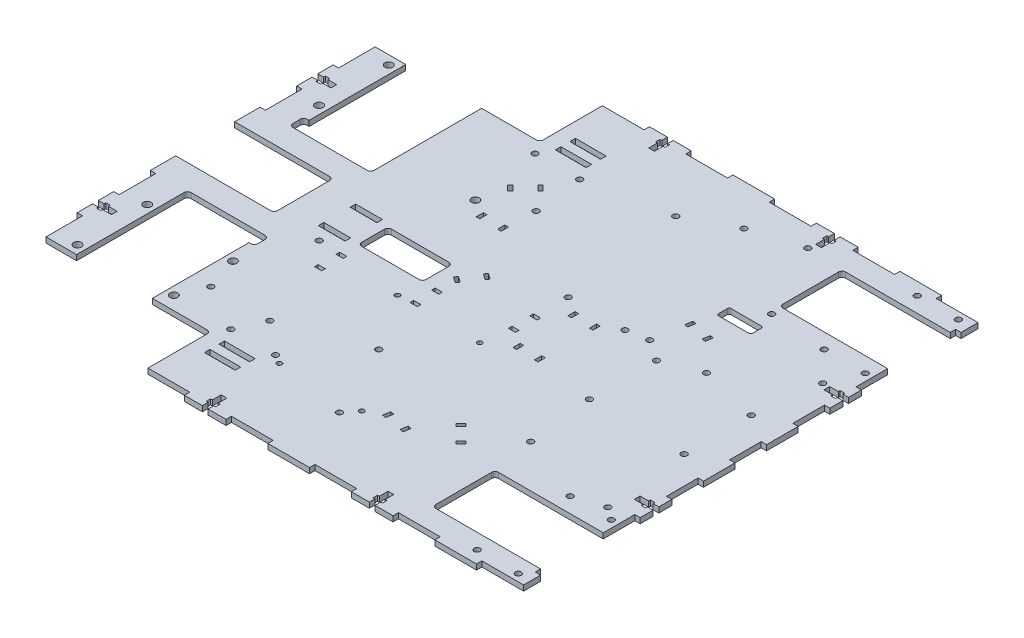
SolidWorks part; units mm, degrees
ref_plane "Front Plane" through (0, 0, 0) normal (0, 0, 1) x (1, 0, 0)
ref_plane "Top Plane" through (0, 0, 0) normal (0, 1, 0) x (1, 0, 0)
ref_plane "Right Plane" through (0, 0, 0) normal (1, 0, 0) x (0, 0, -1)
sketch "Sketch1" plane through (0, 0, 0) normal (0, 1, 0) x (1, 0, 0)
  line L0 (-152.5, 92) -> (-57.5, 92)
  line L5 (-57.5, 92) -> (-57.5, 130)
  line L6 (-57.5, 130) -> (152.5, 130)
  line L7 (152.5, 130) -> (152.5, -130)
  line L8 (152.5, -130) -> (-57.5, -130)
  line L9 (-57.5, -130) -> (-57.5, -92)
  line L10 (-57.5, -92) -> (-152.5, -92)
  line L11 (-152.5, -92) -> (-152.5, 92)
  line L12 (-152.5, 0) -> (152.5, 0) construction
  line L13 (134, -97) -> (134, 97) construction
  line L14 (89, 79.5) -> (152.5, 79.5)
  line L15 (89, 79.5) -> (89, 114.5)
  line L16 (89, 114.5) -> (152.5, 114.5)
  line L17 (152.5, 79.5) -> (152.5, 114.5)
  line L18 (89, 79.5) -> (152.5, 114.5) construction
  line L19 (89, 114.5) -> (152.5, 79.5) construction
  line L20 (89, -114.5) -> (152.5, -114.5)
  line L21 (89, -114.5) -> (89, -79.5)
  line L22 (89, -79.5) -> (152.5, -79.5)
  line L23 (152.5, -114.5) -> (152.5, -79.5)
  line L24 (89, -114.5) -> (152.5, -79.5) construction
  line L25 (89, -79.5) -> (152.5, -114.5) construction
  line L26 (145.5, 71) -> (122.5, 71) construction
  line L27 (145.5, 71) -> (145.5, 123) construction
  line L28 (145.5, 123) -> (122.5, 123) construction
  line L29 (122.5, 71) -> (122.5, 123) construction
  line L30 (145.5, 71) -> (122.5, 123) construction
  line L31 (145.5, 123) -> (122.5, 71) construction
  line L32 (122.5, -123) -> (145.5, -123) construction
  line L33 (122.5, -123) -> (122.5, -71) construction
  line L34 (122.5, -71) -> (145.5, -71) construction
  line L35 (145.5, -123) -> (145.5, -71) construction
  line L36 (122.5, -123) -> (145.5, -71) construction
  line L37 (122.5, -71) -> (145.5, -123) construction
  line L38 (-111.2, 92) -> (-111.2, -92) construction
  line L40 (-132.3981, -30) -> (-90.0019, -30)
  line L41 (-132.3981, -30) -> (-132.3981, -92)
  line L42 (-132.3981, -92) -> (-90.0019, -92)
  line L43 (-90.0019, -30) -> (-90.0019, -92)
  line L44 (-132.3981, -30) -> (-90.0019, -92) construction
  line L45 (-132.3981, -92) -> (-90.0019, -30) construction
  line L50 (-135.3981, 30) -> (-132.3981, 30)
  line L52 (-132.3981, 30) -> (-90.0019, 30)
  line L53 (-132.3981, 30) -> (-132.3981, 92)
  line L54 (-132.3981, 92) -> (-90.0019, 92)
  line L55 (-90.0019, 30) -> (-90.0019, 92)
  line L56 (-132.3981, 30) -> (-90.0019, 92) construction
  line L57 (-132.3981, 92) -> (-90.0019, 30) construction
  line L58 (-135.3981, 30) -> (-135.3981, 38)
  line L59 (-135.3981, 38) -> (-132.3981, 38)
  line L64 (-132.3981, 30) -> (-132.3981, 38)
  line L65 (-87.0019, -38) -> (-90.0019, -38)
  line L86 (-135.3981, 30) -> (-132.3981, 38) construction
  line L87 (-135.3981, 38) -> (-132.3981, 30) construction
  line L88 (-87.0019, -38) -> (-87.0019, -30)
  line L89 (-87.0019, -30) -> (-90.0019, -30)
  line L90 (-90.0019, -38) -> (-90.0019, -30)
  line L91 (-87.0019, -38) -> (-90.0019, -30) construction
  line L92 (-87.0019, -30) -> (-90.0019, -38) construction
  circle A0 centre (122.5, 123) radius 1.65
  circle A1 centre (145.5, 123) radius 1.65
  circle A2 centre (145.5, 71) radius 1.65
  circle A3 centre (122.5, 71) radius 1.65
  circle A4 centre (122.5, -71) radius 1.65
  circle A5 centre (145.5, -71) radius 1.65
  circle A6 centre (122.5, -123) radius 1.65
  circle A7 centre (145.5, -123) radius 1.65
  point P5 (134, 97)
  point P8 (-152.5, 0)
  point P10 (152.5, 0)
  point P12 (0, 0)
  point P13 (120.75, 97)
  point P20 (120.75, -97)
  point P30 (134, -97)
  point P44 (134, 0)
  point P47 (-111.2, -61)
  point P52 (-88.5019, -34)
  point P54 (-133.8981, 34)
  point P61 (-111.2, 61)
  dimension "D11" = 3.3
  dimension "D1" = 305
  dimension "D2" = 260
  dimension "D3" = 38
  dimension "D4" = 95
  dimension "D5" = 35
  dimension "D6" = 52
  dimension "D7" = 23
  dimension "D8" = 7
  dimension "D9" = 7
  dimension "D10" = 45
  dimension "D12" = 41.3
  dimension "D13" = 42.3962
  dimension "D14" = 3
  dimension "D15" = 8
  dimension "D16" = 62
  dimension "D18" = 42.3962
  dimension "D19" = 21.1981
extrude "Base" add sketch "Sketch1" along normal blind 3 contours L21 L22 L7 L14 L15 L16 L6 L5 L0 L11 L10 L9 L8 L20 A7 A6 A5 A4 A3 A2 A1 A0
sketch "Sketch10" plane through (0, 3, 0) normal (0, 1, 0) x (1, 0, 0)
  line L0 (-136.8906, 48) -> (-136.8906, 87) construction
  line L1 (-152.5, 92) -> (-132.3981, 92) construction
  line L2 (-132.3981, 38) -> (-132.3981, 92) construction
  line L4 (-136.8906, -87) -> (-136.8906, -48) construction
  line L5 (-136.8906, -67.5) -> (-132.3981, -67.5) construction
  line L6 (-132.3981, -30) -> (-132.3981, -92) construction
  line L7 (-136.8906, 67.5) -> (-132.3981, 67.5) construction
  line L8 (-136.8906, 87) -> (-136.8906, 92) construction
  line L9 (-136.8906, -87) -> (-136.8906, -92) construction
  line L10 (-132.3981, -92) -> (-152.5, -92) construction
  circle A0 centre (-136.8906, 87) radius 2.175
  circle A1 centre (-136.8906, 48) radius 2.175
  circle A2 centre (-47.3096, 45.8) radius 2.175
  circle A3 centre (-136.8906, -48) radius 2.175
  circle A4 centre (-136.8906, -87) radius 2.175
  circle A5 centre (-85.5093, -84.5) radius 2.175
  circle A6 centre (-85.5093, -51.5) radius 2.175
  dimension "D1" = 4.35
  dimension "D3" = 5
  dimension "D5" = 89.581
  dimension "D6" = 2.2
  dimension "D8" = 2.5
  dimension "D9" = 3.5
  dimension "D2" = 39
  dimension "D4" = 4.4925
  dimension "D7" = 51.3813
extrude "MotorMounts" cut sketch "Sketch10" against normal through all both and the other way through all
sketch "Sketch2" plane through (0, 3, 0) normal (0, 1, 0) x (1, 0, 0)
  line L0 (134, -97) -> (134, 97) construction
  line L1 (81, 18.75) -> (134, 18.75) construction
  line L2 (81, 18.75) -> (81, -18.75) construction
  line L3 (81, -18.75) -> (134, -18.75) construction
  line L4 (134, 18.75) -> (134, -18.75) construction
  line L5 (81, 18.75) -> (134, -18.75) construction
  line L6 (81, -18.75) -> (134, 18.75) construction
  line L9 (138.5, -23.5) -> (76.5, -23.5) construction
  line L10 (138.5, -23.5) -> (138.5, 23.5) construction
  line L11 (138.5, 23.5) -> (76.5, 23.5) construction
  line L12 (76.5, -23.5) -> (76.5, 23.5) construction
  line L13 (138.5, -23.5) -> (76.5, 23.5) construction
  line L14 (138.5, 23.5) -> (76.5, -23.5) construction
  circle A0 centre (81, 18.75) radius 1.65
  circle A1 centre (134, 18.75) radius 1.65
  circle A2 centre (134, -18.75) radius 1.65
  circle A3 centre (81, -18.75) radius 1.65
  point P0 (107.5, 0)
  point P12 (107.5, 0)
  dimension "D3" = 3.3
  dimension "D1" = 37.5
  dimension "D2" = 53
  dimension "D4" = 47
  dimension "D5" = 62
extrude "LineFollow" cut sketch "Sketch2" against normal through all both and the other way through all
sketch "Sketch3" plane through (0, 3, 0) normal (0, 1, 0) x (1, 0, 0)
  line L0 (64.76, 59.286) -> (143.5, 59.286) construction
  line L1 (143.5, 59.286) -> (143.5, -70) construction
  line L2 (143.5, -70) -> (71.491, -70) construction
  line L3 (71.491, -70) -> (64.76, -63.269) construction
  line L4 (64.76, -63.269) -> (64.76, 59.286) construction
  line L5 (69.205, 26.774) -> (100.955, 26.774) construction
  line L6 (85.08, -55.649) -> (85.08, 26.774) construction
  line L7 (138.42, 59.286) -> (138.42, 54.206) construction
  line L8 (138.42, 54.206) -> (143.5, 54.206) construction
  line L9 (143.5, -65.809) -> (138.42, -65.809) construction
  line L10 (138.42, -65.809) -> (138.42, -70) construction
  line L12 (152.5, 79.5) -> (152.5, -79.5) construction
  line L13 (76.64, 57.786) -> (93.64, 57.786)
  line L14 (75.64, 58.786) -> (75.64, 63.786)
  line L15 (76.64, 64.786) -> (93.64, 64.786)
  line L16 (94.64, 58.786) -> (94.64, 63.786)
  line L17 (75.64, 57.786) -> (94.64, 64.786) construction
  line L18 (75.64, 64.786) -> (94.64, 57.786) construction
  circle A0 centre (69.205, 26.774) radius 1.65
  circle A1 centre (100.955, 26.774) radius 1.65
  circle A2 centre (85.08, -55.649) radius 1.65
  circle A3 centre (138.42, 54.206) radius 1.65
  circle A4 centre (138.42, -65.809) radius 1.65
  arc A5 (76.64, 57.786) -> (75.64, 58.786) centre (76.64, 58.786) cw
  arc A6 (93.64, 57.786) -> (94.64, 58.786) centre (93.64, 58.786) ccw
  arc A7 (93.64, 64.786) -> (94.64, 63.786) centre (93.64, 63.786) cw
  arc A8 (75.64, 63.786) -> (76.64, 64.786) centre (76.64, 63.786) cw
  point P4 (85.14, 61.286)
  dimension "D5" = 3.3
  dimension "D18" = 1
  dimension "D1" = 78.74
  dimension "D2" = 129.286
  dimension "D3" = 135
  dimension "D4" = 6.731
  dimension "D6" = 31.75
  dimension "D7" = 82.423
  dimension "D8" = 32.512
  dimension "D9" = 4.445
  dimension "D10" = 5.08
  dimension "D11" = 4.191
  dimension "D12" = 70
  dimension "D13" = 9
  dimension "D14" = 19
  dimension "D15" = 7
  dimension "D16" = 1.5
  dimension "D17" = 20.38
extrude "Mobo" cut sketch "Sketch3" against normal through all both and the other way through all
sketch "Sketch4" plane through (0, 3, 0) normal (0, 1, 0) x (1, 0, 0)
  line L0 (41.553, 107.122) -> (41.553, 24.699) construction
  line L1 (21.106, 121.473) -> (62, 121.473) construction
  line L2 (21.106, 121.473) -> (21.106, 20) construction
  line L3 (21.106, 20) -> (62, 20) construction
  line L4 (62, 121.473) -> (62, 20) construction
  line L5 (21.106, 121.473) -> (62, 20) construction
  line L6 (21.106, 20) -> (62, 121.473) construction
  line L7 (25.678, 24.699) -> (57.428, 24.699) construction
  line L8 (89, 79.5) -> (89, 114.5) construction
  line L9 (-57.5, 130) -> (152.5, 130) construction
  line L10 (-152.5, 0) -> (152.5, 0) construction
  line L11 (-152.5, -92) -> (-152.5, 92) construction
  line L12 (152.5, 79.5) -> (152.5, -79.5) construction
  circle A0 centre (25.678, 24.699) radius 1.65
  circle A1 centre (57.428, 24.699) radius 1.65
  circle A2 centre (41.553, 107.122) radius 1.65
  point P0 (41.553, 70.7365)
  point P9 (41.553, 24.699)
  dimension "D3" = 3.3
  dimension "D1" = 31.75
  dimension "D2" = 82.423
  dimension "D4" = 40.894
  dimension "D5" = 101.473
  dimension "D6" = 4.699
  dimension "D7" = 27
  dimension "D8" = 110
extrude "HBridge" cut sketch "Sketch4" against normal through all both and the other way through all
sketch "Sketch6" plane through (0, 3, 0) normal (0, 1, 0) x (1, 0, 0)
  line L0 (-152.5, -92) -> (-152.5, 92) construction
  line L1 (-58.6638, -8.35) -> (-22.6638, -8.35)
  line L2 (-58.6638, -8.35) -> (-58.6638, 8.35)
  line L3 (-58.6638, 8.35) -> (-22.6638, 8.35)
  line L4 (-22.6638, -8.35) -> (-22.6638, 8.35)
  line L5 (-58.6638, -8.35) -> (-22.6638, 8.35) construction
  line L6 (-58.6638, 8.35) -> (-22.6638, -8.35) construction
  point P0 (-40.6638, 0)
  dimension "D1" = 111.8362
  dimension "D3" = 16.7
  dimension "D6" = 36
extrude "GearClearence" cut sketch "Sketch6" against normal through all both and the other way through all
sketch "Sketch7" plane through (0, 3, 0) normal (0, 1, 0) x (1, 0, 0)
  line L1 (-40.6638, 94.05) -> (-40.6638, 102.15) construction
  line L2 (-78.8576, 10.4502) -> (-63.8576, 10.4502)
  line L4 (-78.8576, 10.4502) -> (-78.8576, 7.3502)
  line L9 (-78.8576, 7.3502) -> (-63.8576, 7.3502)
  line L10 (-63.8576, 10.4502) -> (-63.8576, 7.3502)
  line L15 (-78.8576, 10.4502) -> (-63.8576, 7.3502) construction
  line L16 (-78.8576, 7.3502) -> (-63.8576, 10.4502) construction
  line L21 (-78.8576, -7.3502) -> (-63.8576, -7.3502)
  line L22 (-78.8576, -7.3502) -> (-78.8576, -10.4502)
  line L27 (-78.8576, -10.4502) -> (-63.8576, -10.4502)
  line L28 (-63.8576, -7.3502) -> (-63.8576, -10.4502)
  line L29 (-78.8576, -7.3502) -> (-63.8576, -10.4502) construction
  line L30 (-78.8576, -10.4502) -> (-63.8576, -7.3502) construction
  line L32 (-49.2426, 103.7) -> (-32.0849, 103.7)
  line L33 (-49.2426, 103.7) -> (-49.2426, 100.6)
  line L40 (-49.2426, 100.6) -> (-32.0849, 100.6)
  line L45 (-32.0849, 103.7) -> (-32.0849, 100.6)
  line L62 (-49.2426, 103.7) -> (-32.0849, 100.6) construction
  line L63 (-49.2426, 100.6) -> (-32.0849, 103.7) construction
  line L68 (-49.2427, 95.6) -> (-32.085, 95.6)
  line L69 (-49.2427, 95.6) -> (-49.2427, 92.5)
  line L71 (-49.2427, 92.5) -> (-32.085, 92.5)
  line L84 (-32.085, 95.6) -> (-32.085, 92.5)
  line L89 (-49.2427, 95.6) -> (-32.085, 92.5) construction
  line L90 (-49.2427, 92.5) -> (-32.085, 95.6) construction
  line L95 (-49.2427, -92.5) -> (-32.085, -92.5)
  line L96 (-49.2427, -92.5) -> (-49.2427, -95.6)
  line L97 (-49.2427, -95.6) -> (-32.085, -95.6)
  line L102 (-32.085, -92.5) -> (-32.085, -95.6)
  line L103 (-49.2427, -92.5) -> (-32.085, -95.6) construction
  line L104 (-49.2427, -95.6) -> (-32.085, -92.5) construction
  line L105 (-49.2426, -103.7) -> (-32.0849, -103.7)
  line L106 (-49.2426, -103.7) -> (-49.2426, -100.6)
  line L107 (-49.2426, -100.6) -> (-32.0849, -100.6)
  line L108 (-32.0849, -103.7) -> (-32.0849, -100.6)
  line L109 (-49.2426, -103.7) -> (-32.0849, -100.6) construction
  line L110 (-49.2426, -100.6) -> (-32.0849, -103.7) construction
  line L111 (-40.6638, 94.05) -> (-40.6638, -94.05) construction
  line L112 (-40.6638, -94.05) -> (-40.6638, -102.15) construction
  line L113 (-71.3576, -8.9002) -> (-71.3576, 8.9002) construction
  line L114 (-58.6638, 8.35) -> (-22.6638, 8.35) construction
  line L115 (-53.1638, -85) -> (-28.1638, -85) construction
  line L116 (-53.1638, 85) -> (-28.1638, 85) construction
  line L117 (-40.6638, 85) -> (-40.6638, 92.5) construction
  line L118 (-40.6638, -85) -> (-40.6638, -92.5) construction
  circle A6 centre (-53.1638, 85) radius 1.65
  circle A7 centre (-28.1638, 85) radius 1.65
  circle A8 centre (-28.1638, -85) radius 1.65
  circle A9 centre (-53.1638, -85) radius 1.65
  circle A10 centre (-71.3576, -17.4503) radius 1.65
  point P0 (-71.3576, 8.9002)
  point P5 (-71.3576, -8.9002)
  point P10 (-40.6638, 102.15)
  point P15 (-40.6638, 94.05)
  point P20 (-40.6638, -94.05)
  point P25 (-40.6638, -102.15)
  point P32 (-40.6638, 0)
  point P38 (-71.3576, 0)
  point P42 (-40.6638, 8.35)
  point P52 (-40.6638, -85)
  point P53 (-40.6638, 85)
  dimension "D8" = 3.3
  dimension "D1" = 3.1
  dimension "D2" = 17.1577
  dimension "D3" = 185
  dimension "D4" = 5
  dimension "D5" = 15
  dimension "D6" = 14.7005
  dimension "D7" = 23.1938
  dimension "D9" = 7.5
  dimension "D10" = 25
  dimension "D11" = 7
extrude "GearMounting" cut sketch "Sketch7" against normal through all both and the other way through all
sketch "Sketch5" plane through (0, 3, 0) normal (0, 1, 0) x (1, 0, 0)
  line L0 (-152.5, -92) -> (-152.5, 92) construction
  line L1 (-152.5, 92) -> (-149.5, 92)
  line L2 (-152.5, 92) -> (-152.5, 71.5556)
  line L3 (-152.5, 71.5556) -> (-149.5, 71.5556)
  line L4 (-149.5, 92) -> (-149.5, 71.5556)
  line L5 (-152.5, 51.1111) -> (-149.5, 51.1111)
  line L6 (-152.5, 51.1111) -> (-152.5, 30.6667)
  line L7 (-152.5, 30.6667) -> (-149.5, 30.6667)
  line L8 (-149.5, 51.1111) -> (-149.5, 30.6667)
  line L9 (-132.3981, -92) -> (-152.5, -92) construction
  line L10 (-152.5, 10.2222) -> (-149.5, 10.2222)
  line L11 (-152.5, 10.2222) -> (-152.5, -10.2222)
  line L12 (-152.5, -10.2222) -> (-149.5, -10.2222)
  line L13 (-149.5, 10.2222) -> (-149.5, -10.2222)
  line L14 (-152.5, -30.6667) -> (-149.5, -30.6667)
  line L15 (-152.5, -30.6667) -> (-152.5, -51.1111)
  line L16 (-152.5, -51.1111) -> (-149.5, -51.1111)
  line L17 (-149.5, -30.6667) -> (-149.5, -51.1111)
  line L18 (-152.5, -71.5556) -> (-149.5, -71.5556)
  line L19 (-152.5, -71.5556) -> (-152.5, -92)
  line L20 (-152.5, -92) -> (-149.5, -92)
  line L21 (-149.5, -71.5556) -> (-149.5, -92)
  line L22 (-149.5, 71.5556) -> (-149.5, 51.1111) construction
  line L23 (-149.5, 30.6667) -> (-149.5, 10.2222) construction
  line L24 (-149.5, -10.2222) -> (-149.5, -30.6667) construction
  line L25 (-149.5, -51.1111) -> (-149.5, -71.5556) construction
  line L26 (152.5, 79.5) -> (152.5, -79.5) construction
  line L27 (152.5, 79.5) -> (149.5, 79.5)
  line L28 (152.5, 79.5) -> (152.5, 61.8333)
  line L29 (152.5, 61.8333) -> (149.5, 61.8333)
  line L30 (149.5, 79.5) -> (149.5, 61.8333)
  line L31 (152.5, 44.1667) -> (149.5, 44.1667)
  line L32 (152.5, 44.1667) -> (152.5, 26.5)
  line L33 (152.5, 26.5) -> (149.5, 26.5)
  line L34 (149.5, 44.1667) -> (149.5, 26.5)
  line L35 (149.5, 61.8333) -> (149.5, 44.1667) construction
  line L36 (152.5, 8.8333) -> (149.5, 8.8333)
  line L37 (152.5, 8.8333) -> (152.5, -8.8333)
  line L38 (152.5, -8.8333) -> (149.5, -8.8333)
  line L39 (149.5, 8.8333) -> (149.5, -8.8333)
  line L40 (152.5, -26.5) -> (149.5, -26.5)
  line L41 (152.5, -26.5) -> (152.5, -44.1667)
  line L42 (152.5, -44.1667) -> (149.5, -44.1667)
  line L43 (149.5, -26.5) -> (149.5, -44.1667)
  line L44 (152.5, -79.5) -> (149.5, -79.5)
  line L45 (152.5, -79.5) -> (152.5, -61.8333)
  line L46 (152.5, -61.8333) -> (149.5, -61.8333)
  line L47 (149.5, -79.5) -> (149.5, -61.8333)
  line L48 (149.5, 26.5) -> (149.5, 8.8333) construction
  line L49 (149.5, -8.8333) -> (149.5, -26.5) construction
  line L50 (149.5, -44.1667) -> (149.5, -61.8333) construction
  line L51 (-57.5, 130) -> (152.5, 130) construction
  line L52 (-57.5, 130) -> (-34.1667, 130)
  line L53 (-57.5, 130) -> (-57.5, 127)
  line L54 (-57.5, 127) -> (-34.1667, 127)
  line L55 (-34.1667, 130) -> (-34.1667, 127)
  line L56 (-10.8333, 130) -> (12.5, 130)
  line L57 (-10.8333, 130) -> (-10.8333, 127)
  line L58 (-10.8333, 127) -> (12.5, 127)
  line L59 (12.5, 130) -> (12.5, 127)
  line L60 (152.5, 130) -> (152.5, 114.5) construction
  line L61 (35.8333, 130) -> (59.1667, 130)
  line L62 (35.8333, 130) -> (35.8333, 127)
  line L63 (35.8333, 127) -> (59.1667, 127)
  line L64 (59.1667, 130) -> (59.1667, 127)
  line L65 (82.5, 130) -> (105.8333, 130)
  line L66 (82.5, 130) -> (82.5, 127)
  line L67 (82.5, 127) -> (105.8333, 127)
  line L68 (105.8333, 130) -> (105.8333, 127)
  line L69 (129.1667, 130) -> (152.5, 130)
  line L70 (129.1667, 130) -> (129.1667, 127)
  line L71 (129.1667, 127) -> (152.5, 127)
  line L72 (152.5, 130) -> (152.5, 127)
  line L73 (-34.1667, 127) -> (-10.8333, 127) construction
  line L74 (12.5, 127) -> (35.8333, 127) construction
  line L75 (59.1667, 127) -> (82.5, 127) construction
  line L76 (105.8333, 127) -> (129.1667, 127) construction
  line L77 (89, 114.5) -> (152.5, 114.5) construction
  line L78 (152.5, 117.5) -> (149.5, 117.5)
  line L79 (152.5, 117.5) -> (152.5, 114.5)
  line L80 (152.5, 114.5) -> (149.5, 114.5)
  line L81 (149.5, 117.5) -> (149.5, 114.5)
  line L82 (-1.65, 0) -> (1.65, 0) construction
  line L83 (105.8333, -127) -> (129.1667, -127) construction
  line L84 (59.1667, -127) -> (82.5, -127) construction
  line L85 (12.5, -127) -> (35.8333, -127) construction
  line L86 (-34.1667, -127) -> (-10.8333, -127) construction
  line L87 (149.5, -117.5) -> (149.5, -114.5)
  line L88 (152.5, -114.5) -> (149.5, -114.5)
  line L89 (152.5, -117.5) -> (152.5, -114.5)
  line L90 (152.5, -117.5) -> (149.5, -117.5)
  line L91 (152.5, -130) -> (152.5, -127)
  line L92 (129.1667, -127) -> (152.5, -127)
  line L93 (129.1667, -130) -> (129.1667, -127)
  line L94 (129.1667, -130) -> (152.5, -130)
  line L95 (105.8333, -130) -> (105.8333, -127)
  line L96 (82.5, -127) -> (105.8333, -127)
  line L97 (82.5, -130) -> (82.5, -127)
  line L98 (82.5, -130) -> (105.8333, -130)
  line L99 (59.1667, -130) -> (59.1667, -127)
  line L100 (35.8333, -127) -> (59.1667, -127)
  line L101 (35.8333, -130) -> (35.8333, -127)
  line L102 (35.8333, -130) -> (59.1667, -130)
  line L103 (12.5, -130) -> (12.5, -127)
  line L104 (-10.8333, -127) -> (12.5, -127)
  line L105 (-10.8333, -130) -> (-10.8333, -127)
  line L106 (-10.8333, -130) -> (12.5, -130)
  line L107 (-34.1667, -130) -> (-34.1667, -127)
  line L108 (-57.5, -127) -> (-34.1667, -127)
  line L109 (-57.5, -130) -> (-57.5, -127)
  line L110 (-57.5, -130) -> (-34.1667, -130)
  dimension "D1" = 3
extrude "FingerJoints" cut sketch "Sketch5" against normal through all both and the other way through all
sketch "Sketch8" plane through (0, 3, 0) normal (0, 1, 0) x (1, 0, 0)
  line L0 (-34.1667, 130) -> (-10.8333, 130) construction
  line L1 (-24.1, 119.5) -> (-20.9, 119.5)
  line L2 (-24.1, 119.5) -> (-24.1, 130)
  line L3 (-24.1, 130) -> (-20.9, 130)
  line L4 (-20.9, 119.5) -> (-20.9, 130)
  line L5 (-24.1, 119.5) -> (-20.9, 130) construction
  line L6 (-24.1, 130) -> (-20.9, 119.5) construction
  line L7 (59.1667, 130) -> (82.5, 130) construction
  line L8 (69.2333, 119.5) -> (72.4333, 119.5)
  line L9 (69.2333, 119.5) -> (69.2333, 130)
  line L10 (69.2333, 130) -> (72.4333, 130)
  line L11 (72.4333, 119.5) -> (72.4333, 130)
  line L12 (69.2333, 119.5) -> (72.4333, 130) construction
  line L13 (69.2333, 130) -> (72.4333, 119.5) construction
  line L14 (82.5, -130) -> (59.1667, -130) construction
  line L15 (72.4333, -119.5) -> (69.2333, -119.5)
  line L16 (72.4333, -119.5) -> (72.4333, -130)
  line L17 (72.4333, -130) -> (69.2333, -130)
  line L18 (69.2333, -119.5) -> (69.2333, -130)
  line L19 (72.4333, -119.5) -> (69.2333, -130) construction
  line L20 (72.4333, -130) -> (69.2333, -119.5) construction
  line L21 (-10.8333, -130) -> (-34.1667, -130) construction
  line L22 (-24.1, -119.5) -> (-20.9, -119.5)
  line L23 (-24.1, -119.5) -> (-24.1, -130)
  line L24 (-24.1, -130) -> (-20.9, -130)
  line L25 (-20.9, -119.5) -> (-20.9, -130)
  line L26 (-24.1, -119.5) -> (-20.9, -130) construction
  line L27 (-24.1, -130) -> (-20.9, -119.5) construction
  line L28 (152.5, 61.8333) -> (152.5, 44.1667) construction
  line L29 (142, 54.6) -> (152.5, 54.6)
  line L30 (142, 54.6) -> (142, 51.4)
  line L31 (142, 51.4) -> (152.5, 51.4)
  line L32 (152.5, 54.6) -> (152.5, 51.4)
  line L33 (142, 54.6) -> (152.5, 51.4) construction
  line L34 (142, 51.4) -> (152.5, 54.6) construction
  line L35 (152.5, -44.1667) -> (152.5, -61.8333) construction
  line L36 (142, -51.4) -> (152.5, -51.4)
  line L37 (142, -51.4) -> (142, -54.6)
  line L38 (142, -54.6) -> (152.5, -54.6)
  line L39 (152.5, -51.4) -> (152.5, -54.6)
  line L40 (142, -51.4) -> (152.5, -54.6) construction
  line L41 (142, -54.6) -> (152.5, -51.4) construction
  line L42 (-152.5, 51.1111) -> (-152.5, 71.5556) construction
  line L43 (-142, 59.7333) -> (-152.5, 59.7333)
  line L44 (-142, 59.7333) -> (-142, 62.9333)
  line L45 (-142, 62.9333) -> (-152.5, 62.9333)
  line L46 (-152.5, 59.7333) -> (-152.5, 62.9333)
  line L47 (-142, 59.7333) -> (-152.5, 62.9333) construction
  line L48 (-142, 62.9333) -> (-152.5, 59.7333) construction
  line L49 (-152.5, -71.5556) -> (-152.5, -51.1111) construction
  line L50 (-142, -62.9333) -> (-152.5, -62.9333)
  line L51 (-142, -62.9333) -> (-142, -59.7333)
  line L52 (-142, -59.7333) -> (-152.5, -59.7333)
  line L53 (-152.5, -62.9333) -> (-152.5, -59.7333)
  line L54 (-142, -62.9333) -> (-152.5, -59.7333) construction
  line L55 (-142, -59.7333) -> (-152.5, -62.9333) construction
  line L56 (-22.5, 125.575) -> (-22.5, 130) construction
  line L57 (-25.1, 124.325) -> (-19.9, 124.325)
  line L58 (-25.1, 124.325) -> (-25.1, 126.825)
  line L59 (-25.1, 126.825) -> (-19.9, 126.825)
  line L60 (-19.9, 124.325) -> (-19.9, 126.825)
  line L61 (-25.1, 124.325) -> (-19.9, 126.825) construction
  line L62 (-25.1, 126.825) -> (-19.9, 124.325) construction
  line L63 (68.2333, 126.825) -> (73.4333, 126.825)
  line L64 (68.2333, 126.825) -> (68.2333, 124.325)
  line L65 (68.2333, 124.325) -> (73.4333, 124.325)
  line L66 (73.4333, 126.825) -> (73.4333, 124.325)
  line L67 (68.2333, 126.825) -> (73.4333, 124.325) construction
  line L68 (68.2333, 124.325) -> (73.4333, 126.825) construction
  line L69 (149.325, 50.4) -> (146.825, 50.4)
  line L70 (149.325, 50.4) -> (149.325, 55.6)
  line L71 (149.325, 55.6) -> (146.825, 55.6)
  line L72 (146.825, 50.4) -> (146.825, 55.6)
  line L73 (149.325, 50.4) -> (146.825, 55.6) construction
  line L74 (149.325, 55.6) -> (146.825, 50.4) construction
  line L75 (149.325, -55.6) -> (146.825, -55.6)
  line L76 (149.325, -55.6) -> (149.325, -50.4)
  line L77 (149.325, -50.4) -> (146.825, -50.4)
  line L78 (146.825, -55.6) -> (146.825, -50.4)
  line L79 (149.325, -55.6) -> (146.825, -50.4) construction
  line L80 (149.325, -50.4) -> (146.825, -55.6) construction
  line L81 (68.2333, -126.825) -> (73.4333, -126.825)
  line L82 (68.2333, -126.825) -> (68.2333, -124.325)
  line L83 (68.2333, -124.325) -> (73.4333, -124.325)
  line L84 (73.4333, -126.825) -> (73.4333, -124.325)
  line L85 (68.2333, -126.825) -> (73.4333, -124.325) construction
  line L86 (68.2333, -124.325) -> (73.4333, -126.825) construction
  line L87 (-25.1, -126.825) -> (-19.9, -126.825)
  line L88 (-25.1, -126.825) -> (-25.1, -124.325)
  line L89 (-25.1, -124.325) -> (-19.9, -124.325)
  line L90 (-19.9, -126.825) -> (-19.9, -124.325)
  line L91 (-25.1, -126.825) -> (-19.9, -124.325) construction
  line L92 (-25.1, -124.325) -> (-19.9, -126.825) construction
  line L93 (-149.325, -58.7333) -> (-146.825, -58.7333)
  line L94 (-149.325, -58.7333) -> (-149.325, -63.9333)
  line L95 (-149.325, -63.9333) -> (-146.825, -63.9333)
  line L96 (-146.825, -58.7333) -> (-146.825, -63.9333)
  line L97 (-149.325, -58.7333) -> (-146.825, -63.9333) construction
  line L98 (-149.325, -63.9333) -> (-146.825, -58.7333) construction
  line L99 (-149.325, 63.9333) -> (-146.825, 63.9333)
  line L100 (-149.325, 63.9333) -> (-149.325, 58.7333)
  line L101 (-149.325, 58.7333) -> (-146.825, 58.7333)
  line L102 (-146.825, 63.9333) -> (-146.825, 58.7333)
  line L103 (-149.325, 63.9333) -> (-146.825, 58.7333) construction
  line L104 (-149.325, 58.7333) -> (-146.825, 63.9333) construction
  line L105 (70.8333, 125.575) -> (70.8333, 130) construction
  line L106 (148.075, 53) -> (152.5, 53) construction
  line L107 (152.5, -53) -> (148.075, -53) construction
  line L108 (70.8333, -130) -> (70.8333, -125.575) construction
  line L109 (-22.5, -130) -> (-22.5, -125.575) construction
  line L110 (-152.5, -61.3333) -> (-148.075, -61.3333) construction
  line L111 (-152.5, 61.3333) -> (-148.075, 61.3333) construction
  point P0 (-22.5, 124.75)
  point P7 (70.8333, 124.75)
  point P14 (70.8333, -124.75)
  point P21 (-22.5, -124.75)
  point P28 (147.25, 53)
  point P35 (147.25, -53)
  point P42 (-147.25, 61.3333)
  point P49 (-147.25, -61.3333)
  point P56 (-22.5, -125.575)
  point P57 (-152.5, 61.3333)
  point P58 (-152.5, -61.3333)
  point P59 (-22.5, -130)
  point P60 (70.8333, -130)
  point P61 (-22.5, 130)
  point P62 (70.8333, 130)
  point P63 (152.5, 53)
  point P64 (152.5, -53)
  point P65 (-22.5, 125.575)
  point P70 (70.8333, 125.575)
  point P75 (148.075, 53)
  point P80 (148.075, -53)
  point P85 (70.8333, -125.575)
  point P94 (-148.075, -61.3333)
  point P99 (-148.075, 61.3333)
  dimension "D1" = 10.5
  dimension "D2" = 3.2
  dimension "D3" = 2.5
  dimension "D4" = 5.2
  dimension "D5" = 3.175
extrude "BoltMounting" cut sketch "Sketch8" against normal through all both and the other way through all contours L45 L102 L43 L44 | L96 L52 L94 L50 | L100 L45 L46 L43 | L102 L99 L100 L45 | L102 L43 L100 L101 | L102 L45 L100 L43 | L57 L2 L1 L4 | L59 L58 L57 L2 | L2 L59 L4 L3 | L9 L10 L11 L8 | L63 L66 L65 L64 | L29 L32 L31 L30 | L71 L72 L69 L70 | L38 L39 L36 L37 | L78 L77 L76 L75 | L18 L17 L16 L15 | L83 L84 L81 L82 | L23 L24 L25 L22 | L89 L90 L87 L88
sketch "Sketch9" plane through (0, 3, 0) normal (0, 1, 0) x (1, 0, 0)
  line L0 (-152.5, 10.2222) -> (-152.5, 30.6667) construction
  line L1 (-152.5, -16.5) -> (-97.5, -16.5)
  line L2 (-152.5, -16.5) -> (-152.5, 16.5)
  line L3 (-152.5, 16.5) -> (-97.5, 16.5)
  line L4 (-97.5, -16.5) -> (-97.5, 16.5)
  line L5 (-152.5, -16.5) -> (-97.5, 16.5) construction
  line L6 (-152.5, 16.5) -> (-97.5, -16.5) construction
  point P0 (-125, 0)
  dimension "D1" = 33
  dimension "D2" = 55
extrude "HookClearence" cut sketch "Sketch9" against normal through all both and the other way through all
sketch "Sketch11" plane through (0, 3, 0) normal (0, 1, 0) x (1, 0, 0)
  line L0 (-79.3388, -70) -> (-46.3388, -70) construction
  line L1 (-40.6638, -92.5) -> (-40.6638, 92.5) construction
  line L2 (-32.085, -92.5) -> (-49.2427, -92.5) construction
  line L3 (-49.2427, 92.5) -> (-32.085, 92.5) construction
  line L6 (-57.5, -92) -> (-90.0019, -92) construction
  circle A0 centre (-79.3388, -70) radius 1.65
  circle A1 centre (-46.3388, -70) radius 1.65
  dimension "D1" = 3.3
  dimension "D2" = 38.675
  dimension "D3" = 33
  dimension "D4" = 22
extrude "PotentiometerMounting" cut sketch "Sketch11" against normal through all both and the other way through all
sketch "Sketch13" plane through (0, 3, 0) normal (0, 1, 0) x (1, 0, 0)
  line L1 (-23, -88) -> (23, -88) construction
  line L2 (-23, -88) -> (-23, -22) construction
  line L3 (-23, -22) -> (23, -22) construction
  line L4 (23, -88) -> (23, -22) construction
  line L5 (-23, -88) -> (23, -22) construction
  line L6 (-23, -22) -> (23, -88) construction
  circle A0 centre (-23, -22) radius 1.35
  circle A1 centre (23, -22) radius 1.35
  circle A2 centre (-23, -88) radius 1.35
  circle A3 centre (23, -88) radius 1.35
  point P0 (0, -55)
  dimension "D1" = 2.7
  dimension "D2" = 66
  dimension "D3" = 46
  dimension "D4" = 55
  dimension "D5" = 0
extrude "PowerBoardMounting" cut sketch "Sketch13" against normal through all both and the other way through all
sketch "Sketch12" plane through (0, 3, 0) normal (0, 1, 0) x (1, 0, 0)
  circle A0 centre (17.5, -95) radius 1.65
  circle A1 centre (-2, -53.5) radius 1.65
  circle A3 centre (23, -88) radius 1.35 construction
  dimension "D2" = 19.5
  dimension "D3" = 3.3
  dimension "D4" = 7
  dimension "D5" = 25
  dimension "D1" = 41.5
extrude "ServoMounting" cut sketch "Sketch12" against normal through all both and the other way through all
sketch "Sketch14" plane through (0, 3, 0) normal (0, 1, 0) x (1, 0, 0)
  line L1 (-57.5, 92) -> (-57.5, 127) construction
  line L4 (-10.8333, 127) -> (12.5, 127) construction
  line L5 (90.65, 79.5) -> (90.65, 64.786) construction
  line L6 (89, 79.5) -> (149.5, 79.5) construction
  line L7 (93.64, 64.786) -> (76.64, 64.786) construction
  line L8 (89, 79.5) -> (89, 114.5) construction
  circle A0 centre (16.5, 94) radius 1.65
  circle A1 centre (-25, 57.5) radius 1.65
  circle A2 centre (90.65, 73.5) radius 1.65
  circle A3 centre (68.85, 115.5) radius 1.65
  point P4 (90.65, 73.5968)
  dimension "D1" = 3.3
  dimension "D8" = 3.3
  dimension "D2" = 36.5
  dimension "D3" = 41.5
  dimension "D4" = 74
  dimension "D5" = 33
  dimension "D6" = 21.8
  dimension "D7" = 42
  dimension "D9" = 6
extrude "BatteryMounting" cut sketch "Sketch14" against normal through all both and the other way through all
sketch "Sketch15" plane through (0, 3, 0) normal (0, 1, 0) x (1, 0, 0)
  line L1 (-60, -19.35) -> (-56, -19.35)
  line L2 (-60, -19.35) -> (-60, -17.35)
  line L3 (-60, -17.35) -> (-56, -17.35)
  line L4 (-56, -19.35) -> (-56, -17.35)
  line L5 (-60, -19.35) -> (-56, -17.35) construction
  line L6 (-60, -17.35) -> (-56, -19.35) construction
  line L7 (-60, -31.35) -> (-56, -31.35)
  line L8 (-60, -31.35) -> (-60, -29.35)
  line L9 (-60, -29.35) -> (-56, -29.35)
  line L10 (-56, -31.35) -> (-56, -29.35)
  line L11 (-60, -31.35) -> (-56, -29.35) construction
  line L12 (-60, -29.35) -> (-56, -31.35) construction
  line L17 (-58.6638, -8.35) -> (-22.6638, -8.35) construction
  line L18 (-38, 40) -> (-26, 40) construction
  line L23 (-39, 42) -> (-37, 42)
  line L24 (-39, 42) -> (-39, 38)
  line L29 (73.4598, 43.7265) -> (74.1544, 47.6657)
  line L30 (73.4598, 43.7265) -> (71.4902, 44.0738)
  line L35 (74.1544, 47.6657) -> (72.1848, 48.013)
  line L36 (71.4902, 44.0738) -> (72.1848, 48.013)
  line L41 (35.553, 17.699) -> (47.553, 17.699) construction
  line L42 (34.553, 19.699) -> (36.553, 19.699)
  line L47 (34.553, 19.699) -> (34.553, 15.699)
  line L48 (34.553, 15.699) -> (36.553, 15.699)
  line L49 (24, 7) -> (28, 7)
  line L50 (24, 7) -> (24, 5)
  line L51 (24, 5) -> (28, 5)
  line L52 (28, 7) -> (28, 5)
  line L53 (24, 7) -> (28, 5) construction
  line L54 (24, 5) -> (28, 7) construction
  line L55 (24, -5) -> (28, -5)
  line L56 (24, -5) -> (24, -7)
  line L57 (24, -7) -> (28, -7)
  line L58 (28, -5) -> (28, -7)
  line L59 (24, -5) -> (28, -7) construction
  line L60 (24, -7) -> (28, -5) construction
  line L61 (73.4598, 43.7265) -> (72.1848, 48.013) construction
  line L62 (26, 6) -> (26, -6) construction
  line L63 (36.553, 19.699) -> (36.553, 15.699)
  line L64 (-58, -18.35) -> (-58, -30.35) construction
  line L65 (-16, -10) -> (-12, -10)
  line L70 (-16, -10) -> (-16, -8)
  line L71 (-12, -10) -> (-12, -8)
  line L76 (-16, -8) -> (-12, -8)
  line L77 (-16, -10) -> (-12, -8) construction
  line L78 (-39, 38) -> (-37, 38)
  line L79 (-37, 42) -> (-37, 38)
  line L80 (-39, 42) -> (-37, 38) construction
  line L81 (-39, 38) -> (-37, 42) construction
  line L82 (-27, 42) -> (-25, 42)
  line L83 (-27, 42) -> (-27, 38)
  line L84 (-27, 38) -> (-25, 38)
  line L85 (-25, 42) -> (-25, 38)
  line L86 (-27, 42) -> (-25, 38) construction
  line L87 (-27, 38) -> (-25, 42) construction
  line L89 (-37.1213, 70.7071) -> (-34.2929, 67.8787)
  line L90 (-37.1213, 70.7071) -> (-35.7071, 72.1213)
  line L91 (-34.2929, 67.8787) -> (-32.8787, 69.2929)
  line L92 (-35.7071, 72.1213) -> (-32.8787, 69.2929)
  line L93 (-37.1213, 70.7071) -> (-32.8787, 69.2929) construction
  line L94 (-34.2929, 67.8787) -> (-35.7071, 72.1213) construction
  line L95 (-45.6066, 62.2218) -> (-42.7782, 59.3934)
  line L96 (-45.6066, 62.2218) -> (-44.1924, 63.636)
  line L97 (-42.7782, 59.3934) -> (-41.364, 60.8076)
  line L98 (-44.1924, 63.636) -> (-41.364, 60.8076)
  line L99 (-45.6066, 62.2218) -> (-41.364, 60.8076) construction
  line L100 (-42.7782, 59.3934) -> (-44.1924, 63.636) construction
  line L101 (-43.4853, 61.5147) -> (-35, 70) construction
  line L102 (-58.6638, 8.35) -> (-22.6638, 8.35) construction
  line L103 (-9.329, 12.328) -> (-6.0524, 10.0337)
  line L104 (-9.329, 12.328) -> (-8.1818, 13.9663)
  line L105 (-6.0524, 10.0337) -> (-4.9052, 11.672)
  line L106 (-8.1818, 13.9663) -> (-4.9052, 11.672)
  line L107 (-9.329, 12.328) -> (-4.9052, 11.672) construction
  line L108 (-6.0524, 10.0337) -> (-8.1818, 13.9663) construction
  line L109 (-16.2119, 2.4982) -> (-12.9353, 0.2039)
  line L110 (-16.2119, 2.4982) -> (-15.0647, 4.1365)
  line L111 (-12.9353, 0.2039) -> (-11.7881, 1.8422)
  line L112 (-15.0647, 4.1365) -> (-11.7881, 1.8422)
  line L113 (-16.2119, 2.4982) -> (-11.7881, 1.8422) construction
  line L114 (-12.9353, 0.2039) -> (-15.0647, 4.1365) construction
  line L115 (-14, 2.1702) -> (-7.1171, 12) construction
  line L116 (-12, -10) -> (-16, -8) construction
  line L117 (-16, -22) -> (-12, -22)
  line L118 (-16, -22) -> (-16, -20)
  line L119 (-12, -22) -> (-12, -20)
  line L120 (-16, -20) -> (-12, -20)
  line L121 (-16, -22) -> (-12, -20) construction
  line L122 (-12, -22) -> (-16, -20) construction
  line L123 (-14, -9) -> (-14, -21) construction
  line L126 (34.553, 19.699) -> (36.553, 15.699) construction
  line L127 (34.553, 15.699) -> (36.553, 19.699) construction
  line L128 (46.553, 19.699) -> (48.553, 19.699)
  line L129 (46.553, 19.699) -> (46.553, 15.699)
  line L130 (46.553, 15.699) -> (48.553, 15.699)
  line L131 (48.553, 19.699) -> (48.553, 15.699)
  line L132 (46.553, 19.699) -> (48.553, 15.699) construction
  line L133 (46.553, 15.699) -> (48.553, 19.699) construction
  line L134 (25.678, 24.699) -> (57.428, 24.699) construction
  line L135 (74.1544, 47.6657) -> (71.4902, 44.0738) construction
  line L140 (85.2775, 41.6427) -> (85.9721, 45.582)
  line L141 (85.2775, 41.6427) -> (83.3079, 41.99)
  line L146 (85.9721, 45.582) -> (84.0025, 45.9293)
  line L147 (83.3079, 41.99) -> (84.0025, 45.9293)
  line L148 (35.553, -13) -> (47.553, -13) construction
  line L149 (34.553, -15) -> (36.553, -15)
  line L150 (34.553, -15) -> (34.553, -11)
  line L151 (34.553, -11) -> (36.553, -11)
  line L152 (36.553, -15) -> (36.553, -11)
  line L153 (34.553, -15) -> (36.553, -11) construction
  line L154 (34.553, -11) -> (36.553, -15) construction
  line L155 (46.553, -15) -> (48.553, -15)
  line L156 (46.553, -15) -> (46.553, -11)
  line L157 (46.553, -11) -> (48.553, -11)
  line L158 (48.553, -15) -> (48.553, -11)
  line L159 (46.553, -15) -> (48.553, -11) construction
  line L160 (46.553, -11) -> (48.553, -15) construction
  line L161 (85.2775, 41.6427) -> (84.0025, 45.9293) construction
  line L162 (85.9721, 45.582) -> (83.3079, 41.99) construction
  line L163 (84.64, 43.786) -> (72.8223, 45.8698) construction
  line L164 (76.64, 57.786) -> (93.64, 57.786) construction
  line L165 (94.64, 58.786) -> (94.64, 63.786) construction
  line L166 (56.8076, -69.136) -> (59.636, -66.3076)
  line L171 (56.8076, -69.136) -> (55.3934, -67.7218)
  line L172 (59.636, -66.3076) -> (58.2218, -64.8934)
  line L177 (55.3934, -67.7218) -> (58.2218, -64.8934)
  line L178 (56.8076, -69.136) -> (58.2218, -64.8934) construction
  line L179 (59.636, -66.3076) -> (55.3934, -67.7218) construction
  line L180 (65.2929, -77.6213) -> (68.1213, -74.7929)
  line L181 (65.2929, -77.6213) -> (63.8787, -76.2071)
  line L182 (68.1213, -74.7929) -> (66.7071, -73.3787)
  line L183 (63.8787, -76.2071) -> (66.7071, -73.3787)
  line L184 (65.2929, -77.6213) -> (66.7071, -73.3787) construction
  line L185 (68.1213, -74.7929) -> (63.8787, -76.2071) construction
  line L186 (66, -75.5) -> (57.5147, -67.0147) construction
  line L187 (89, -79.5) -> (149.5, -79.5) construction
  line L188 (89, -114.5) -> (89, -79.5) construction
  line L189 (32.8198, -84.5595) -> (33.5144, -80.6203)
  line L190 (32.8198, -84.5595) -> (30.8502, -84.2122)
  line L191 (33.5144, -80.6203) -> (31.5448, -80.273)
  line L192 (30.8502, -84.2122) -> (31.5448, -80.273)
  line L193 (32.8198, -84.5595) -> (31.5448, -80.273) construction
  line L194 (33.5144, -80.6203) -> (30.8502, -84.2122) construction
  line L195 (44.6375, -86.6433) -> (45.3321, -82.704)
  line L196 (44.6375, -86.6433) -> (42.6679, -86.296)
  line L197 (45.3321, -82.704) -> (43.3625, -82.3567)
  line L198 (42.6679, -86.296) -> (43.3625, -82.3567)
  line L199 (44.6375, -86.6433) -> (43.3625, -82.3567) construction
  line L200 (45.3321, -82.704) -> (42.6679, -86.296) construction
  line L201 (44, -84.5) -> (32.1823, -82.4162) construction
  point P0 (-58, -18.35)
  point P5 (-58, -30.35)
  point P10 (-26, 40)
  point P14 (-38, 40)
  point P21 (84.64, 43.786)
  point P22 (72.8223, 45.8698)
  point P30 (35.553, 17.699)
  point P35 (47.553, 17.699)
  point P40 (26, 6)
  point P45 (26, -6)
  point P61 (-14, -9)
  point P62 (-14, -21)
  point P75 (-43.4853, 61.5147)
  point P76 (-35, 70)
  point P91 (-7.1171, 12)
  point P92 (-14, 2.1702)
  point P98 (26, 0)
  point P105 (41.553, 24.699)
  point P106 (41.553, 17.699)
  point P108 (66, -75.5)
  point P113 (57.5147, -67.0147)
  point P126 (35.553, -13)
  point P131 (47.553, -13)
  point P138 (41.553, -13)
  point P146 (44, -84.5)
  point P147 (32.1823, -82.4162)
  dimension "D1" = 2
  dimension "D2" = 4
  dimension "D3" = 10
  dimension "D4" = 60
  dimension "D5" = 17.35
  dimension "D6" = 40
  dimension "D7" = 25
  dimension "D8" = 70
  dimension "D9" = 35
  dimension "D10" = 45
  dimension "D11" = 14
  dimension "D12" = 12
  dimension "D13" = 55
  dimension "D14" = 26
  dimension "D15" = 10
  dimension "D16" = 9
  dimension "D17" = 14
  dimension "D18" = 7
  dimension "D19" = 10
  dimension "D20" = 13
  dimension "D21" = 45
  dimension "D22" = 4
  dimension "D23" = 23
  dimension "D24" = 170
  dimension "D25" = 45
  dimension "D26" = 5
extrude "WireRouting" cut sketch "Sketch15" against normal through all both and the other way through all
fillet "Fillet2" radius 2 18 edges at (-97.5, 1.5, 16.5) (-97.5, 1.5, -16.5) (-132.3981, 1.5, 30) (-90.0019, 1.5, -30) (-57.5, 1.5, -92) (-57.5, 1.5, 92) (89, 1.5, -114.5) (89, 1.5, -79.5) (89, 1.5, 79.5) (89, 1.5, 114.5) (-58.6638, 1.5, 8.35) (-22.6638, 1.5, 8.35) (-58.6638, 1.5, -8.35) (-22.6638, 1.5, -8.35) (-87.0019, 1.5, 38) (-87.0019, 1.5, 30) (-135.3981, 1.5, -30) (-135.3981, 1.5, -38)
